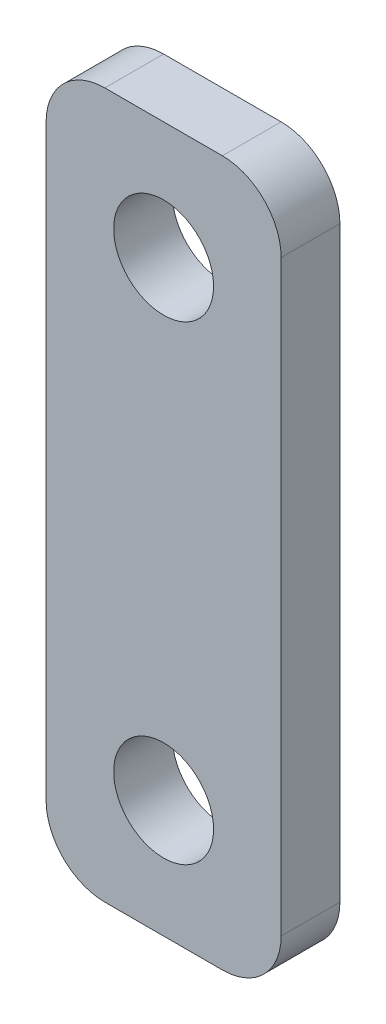
SolidWorks part; units mm, degrees
ref_plane "Plan de face" through (0, 0, 0) normal (0, 0, 1) x (1, 0, 0)
ref_plane "Plan de dessus" through (0, 0, 0) normal (0, 1, 0) x (1, 0, 0)
ref_plane "Plan de droite" through (0, 0, 0) normal (1, 0, 0) x (0, 0, -1)
sketch "Esquisse1" plane through (0, 0, 0) normal (0, 0, 1) x (1, 0, 0)
  line L1 (50, 60) -> (90, 60)
  line L2 (50, 60) -> (50, -60)
  line L3 (50, -60) -> (90, -60)
  line L4 (90, 60) -> (90, -60)
  dimension "D1" = 40
  dimension "D2" = 120
  dimension "D3" = 90
  dimension "D4" = 60
extrude "Boss.-Extru.1" add sketch "Esquisse1" along normal mid plane 10
sketch "Esquisse2" plane through (0, 0, 5) normal (0, 0, 1) x (1, 0, 0)
  line L0 (50, 60) -> (90, 60) construction
  circle A0 centre (70, 40) radius 8.5
  circle A2 centre (70, -40) radius 8.5
  point P7 (70, 60)
  dimension "D1" = 17
  dimension "D2" = 80
  dimension "D3" = 40
  dimension "D4" = 0
extrude "Enlèv. mat.-Extru.1" cut sketch "Esquisse2" against normal through all
fillet "Congé1" radius 10 4 edges at (50, -60, 0) (90, -60, 0) (90, 60, 0) (50, 60, 0)
